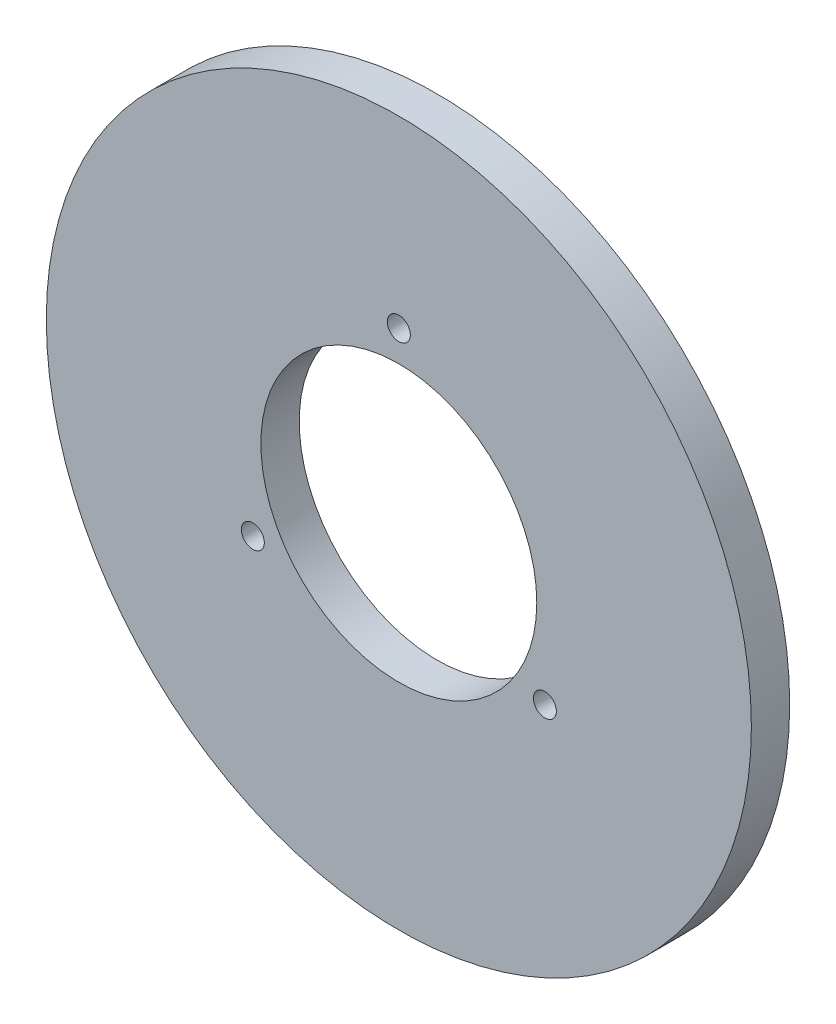
SolidWorks part; units mm, degrees
material "AISI 316 Stainless Steel Sheet (SS)"
ref_plane "Front Plane" through (0, 0, 0) normal (0, 0, 1) x (1, 0, 0)
ref_plane "Top Plane" through (0, 0, 0) normal (0, 1, 0) x (1, 0, 0)
ref_plane "Right Plane" through (0, 0, 0) normal (1, 0, 0) x (0, 0, -1)
sketch "Sketch2" plane through (0, 0, 0) normal (0, 0, 1) x (1, 0, 0)
  circle A0 centre (0, 0) radius 46
  circle A2 centre (0, 0) radius 18
  point P13 (0, 0)
  dimension "D1" = 36
  dimension "D2" = 92
extrude "Boss-Extrude2" add sketch "Sketch2" along normal blind 5
sketch "Sketch5" plane through (0, 0, 0) normal (0, 0, -1) x (-1, 0, 0)
  circle A0 centre (0, 0) radius 22 construction
  circle A1 centre (0, 22) radius 1.5
  circle A2 centre (19.0526, -11) radius 1.5
  circle A3 centre (-19.0526, -11) radius 1.5
  point P11 (0, 0)
  dimension "D1" = 44
  dimension "D2" = 3
  dimension "D3" = 3
extrude "Cut-Extrude1" cut sketch "Sketch5" against normal through all both and the other way through all
